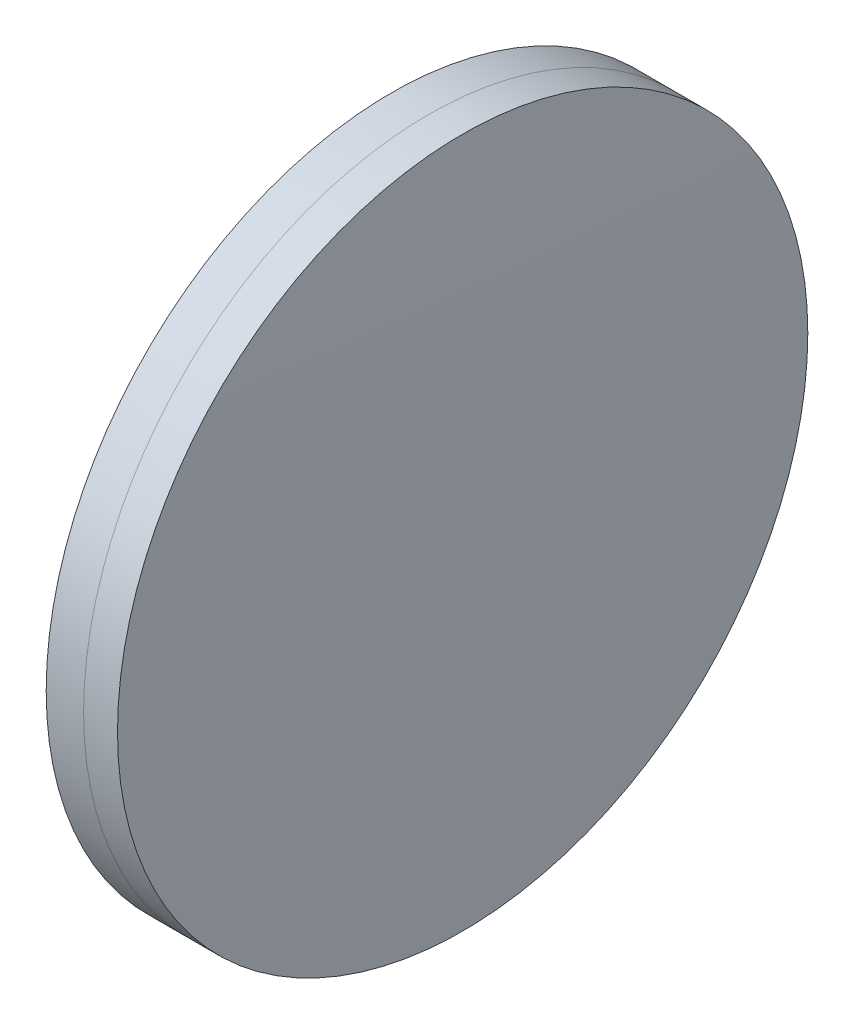
SolidWorks part; units mm, degrees
ref_plane "前视基准面" through (0, 0, 0) normal (0, 0, 1) x (1, 0, 0)
ref_plane "上视基准面" through (0, 0, 0) normal (0, 1, 0) x (1, 0, 0)
ref_plane "右视基准面" through (0, 0, 0) normal (1, 0, 0) x (0, 0, -1)
sketch "草图1" plane through (0, 0, 0) normal (0, 1, 0) x (1, 0, 0)
  line L0 (124.5233, 0) -> (646.9917, 0) construction
  line L1 (610.6585, -25.4) -> (613.4105, -25.4)
  line L2 (610.6585, 25.4) -> (613.4105, 25.4)
  arc A0 (613.4105, -25.4) -> (613.4105, 25.4) centre (216.1216, 0) ccw
  arc A1 (610.6585, 25.4) -> (610.6585, -25.4) centre (1348.7216, 0) ccw
  point P10 (610.2216, 0)
  point P11 (614.2216, 0)
  dimension "D3" = 738.5
  dimension "D4" = 398.1
  dimension "D1" = 25.4
  dimension "D2" = 25.4
  dimension "D5" = 4
revolve "旋转1" add sketch "草图1" angle 360 about L0
sketch "草图2" plane through (0, 0, 0) normal (0, 1, 0) x (1, 0, 0)
  line L0 (-0.5519, 0) -> (622.6607, 0) construction
  line L2 (613.4105, 25.4) -> (615.9063, 25.4)
  line L3 (613.4105, -25.4) -> (615.9063, -25.4)
  arc A0 (615.9063, -25.4) -> (615.9063, 25.4) centre (-407.0784, 0) ccw
  arc A1 (613.4105, -25.4) -> (613.4105, 25.4) centre (216.1216, 0) ccw construction
  arc A2 (613.4105, -25.4) -> (613.4105, 25.4) centre (216.1216, 0) ccw
  point P4 (614.2216, 0)
  point P8 (616.2216, 0)
  dimension "D1" = 1023.3
  dimension "D2" = 2
revolve "旋转3" add sketch "草图2" angle 360 about L0
